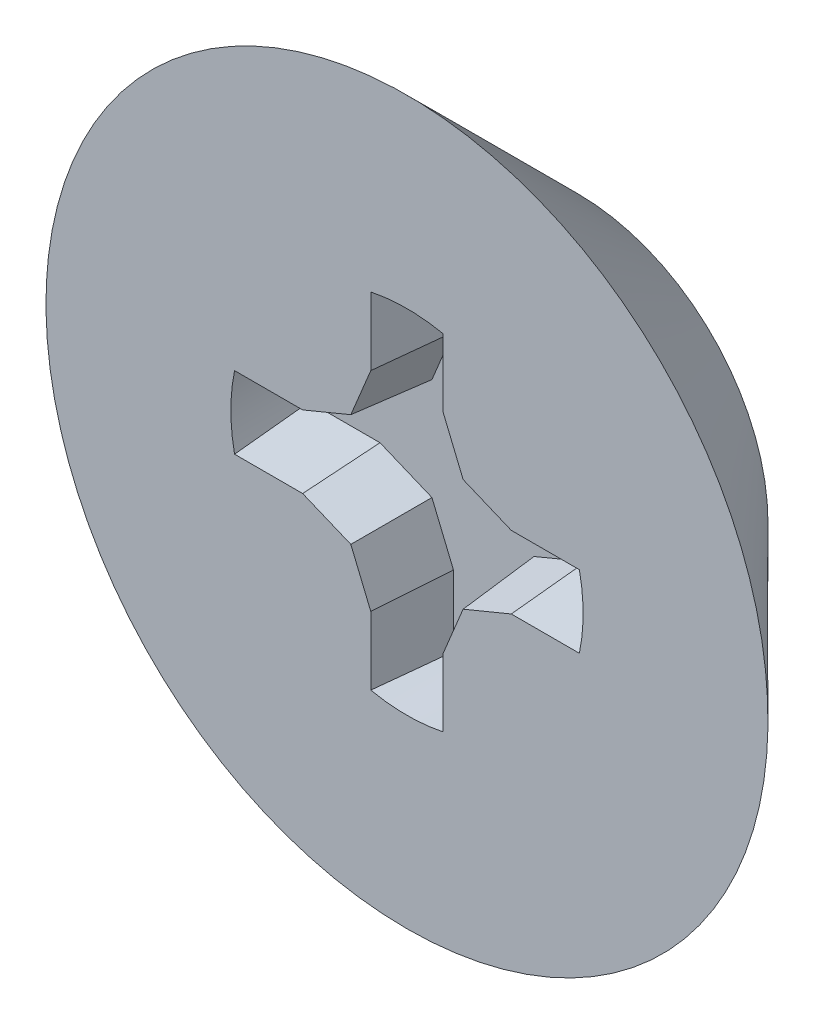
SolidWorks part; units mm, degrees
material "Stainless Steel (ferritic)"
ref_plane "Front Plane" through (0, 0, 0) normal (0, 0, 1) x (1, 0, 0)
ref_plane "Top Plane" through (0, 0, 0) normal (0, 1, 0) x (1, 0, 0)
ref_plane "Right Plane" through (0, 0, 0) normal (1, 0, 0) x (0, 0, -1)
sketch "Sketch1" plane through (0, 0, 0) normal (1, 0, 0) x (0, 0, -1)
  line L0 (0, 0) -> (-1.2, 0) construction
  line L1 (-1.2, 1.9) -> (-1.2, -1.9) construction
  line L2 (-1.2, 1.9) -> (0, 0.7) construction
  line L3 (-1.2, -1.9) -> (0, -0.7) construction
  line L4 (0, 1) -> (0, -1) construction
  line L5 (0, 0) -> (4.8, 0) construction
  line L6 (0, 1) -> (0.4, 1) construction
  line L7 (0, 1) -> (-0.3, 1) construction
  line L8 (4.8, 0.7) -> (4.8, -0.7) construction
  point P6 (-1.2, 0)
  point P11 (0, 0)
  point P16 (-0.3, 1)
  point P17 (3.4, -1)
  point P20 (4.8, 0)
  point P21 (-0.6, 0)
  point P22 (3.4, -0.7)
  point P23 (4.8, -0.7)
  point P25 (4.8, 0.7)
  dimension "Head Height" = 1.2
  dimension "Head Diameter" = 3.8
  dimension "Countersink Angle" = 90
  dimension "Thread OD" = 2
  dimension "Length" = 6
  dimension "Thread Pitch" = 0.4
  dimension "D1" = 1.4
sketch "Sketch2" plane through (0, 0, 0) normal (0, 0, 1) x (1, 0, 0)
  line L0 (0.1905, 0.9271) -> (-0.1905, 0.9271) construction
  circle A0 centre (0, 0) radius 0.9271 construction
  point P3 (0, 0.9271)
  point P7 (0, 0.9271)
  dimension "Drive Dia" = 1.8542
  dimension "Drive Width" = 0.381
sketch "Sketch3" plane through (0, 0, 0) normal (1, 0, 0) x (0, 0, -1)
  line L0 (-1.2, 0) -> (-1.2, 1.9)
  line L1 (-1.2, 1.9) -> (-0.3, 1)
  line L2 (-1.2, 1.9) -> (0, 0.7) construction
  line L3 (0, 1) -> (0.4, 1) construction
  line L4 (-1.2, 0) -> (-0.3, 0)
  line L5 (0, 0) -> (-1.2, 0) construction
  line L6 (-0.3, 0) -> (-0.3, 1)
revolve "Revolve1" add sketch "Sketch3" angle 360 about L4
sketch "Sketch4" plane through (0, 0, 1.2) normal (0, 0, 1) x (1, 0, 0)
  line L0 (0, 0) -> (0, 0.9271)
  line L1 (0, 0) -> (0.9271, 0)
  line L2 (0, 0) -> (0.5489, 0.5489) construction
  line L3 (0.1905, 0.9073) -> (0.1905, 0.5489)
  line L4 (0.1905, 0.5489) -> (0.1905, 0.1905) construction
  line L5 (0.5489, 0.1905) -> (0.1905, 0.1905) construction
  line L6 (0.9073, 0.1905) -> (0.5489, 0.1905)
  line L7 (0.1905, 0.5489) -> (0.2955, 0.2955)
  line L8 (0.2955, 0.2955) -> (0.5489, 0.1905)
  line L9 (0, 0.9271) -> (0, 1.9) construction
  line L10 (0, 1.9) -> (0, -1.9) construction
  circle A0 centre (0, 0) radius 0.9271 construction
  arc A1 (0, 0.9271) -> (0.1905, 0.9073) centre (0, 0) cw
  arc A2 (0.9271, 0) -> (0.9073, 0.1905) centre (0, 0) ccw
  arc A3 (0.5489, 0.1905) -> (0.1905, 0.5489) centre (0.5489, 0.5489) cw construction
  circle A4 centre (0, 0) radius 1.9 construction
  point P8 (0.2955, 0.2955)
  point P22 (0, -0.9271)
  point P23 (0, 0.9271)
  dimension "D1" = 0.9729
extrude "Cut-Extrude1" cut sketch "Sketch4" against normal blind 0.4 contours L1 A2 L6 L8 L7 L3 A1 L0
pattern_circular "CirPattern1" count 4 over 360 about axis through (0, 0, 0) along (0, 0, 1) of "Cut-Extrude1"
draft "Draft2" type of draft neutral plane draft angle 5 faces to draft 16 face at (-0.7281, 0.1905, 1) face at (-0.4222, 0.243, 1) face at (-0.243, 0.4222, 1) face at (-0.1905, 0.7281, 1) face at (0.1905, 0.7281, 1) face at (0.243, 0.4222, 1) face at (0.4222, 0.243, 1) face at (0.7281, 0.1905, 1) face at (0.7281, -0.1905, 1) face at (0.4222, -0.243, 1) face at (0.243, -0.4222, 1) face at (0.1905, -0.7281, 1) face at (-0.1905, -0.7281, 1) face at (-0.243, -0.4222, 1) face at (-0.4222, -0.243, 1) face at (-0.7281, -0.1905, 1) neutral plane through (0, 0, 1.2) neutral plane normal (0, 0, 1) parameters "D1"=5
equation "\"D1@Sketch1\"=\"Thread Pitch@Sketch1\"*3.5"
equation "\"D1@Cut-Extrude1\"=\"Head Height@Sketch1\"/3"
